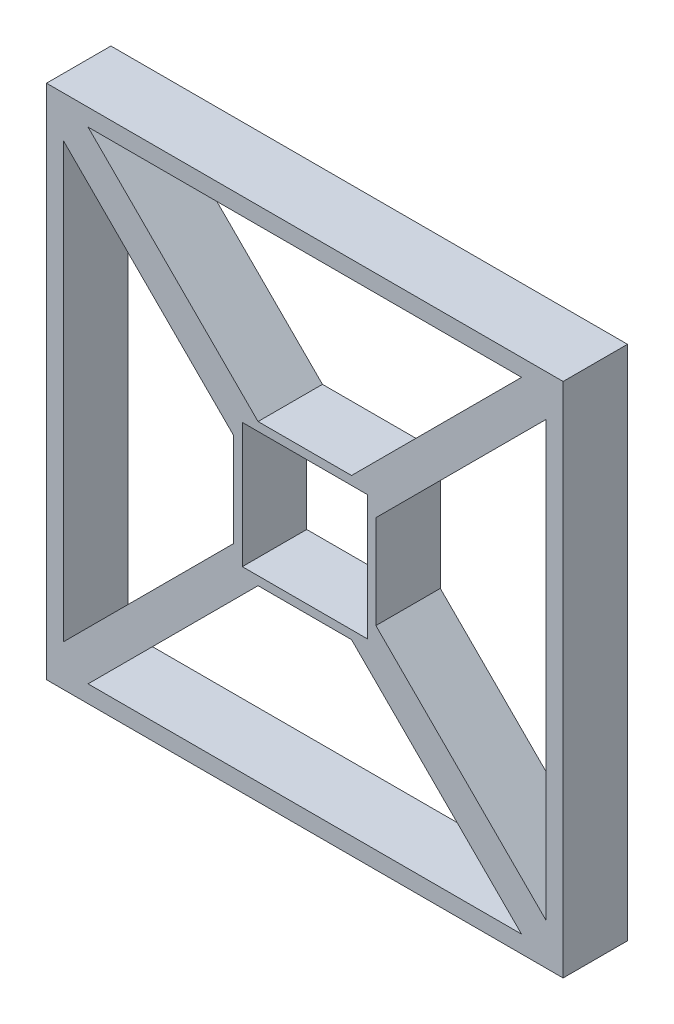
SolidWorks part; units mm, degrees
ref_plane "Front Plane" through (0, 0, 0) normal (0, 0, 1) x (1, 0, 0)
ref_plane "Top Plane" through (0, 0, 0) normal (0, 1, 0) x (1, 0, 0)
ref_plane "Right Plane" through (0, 0, 0) normal (1, 0, 0) x (0, 0, -1)
sketch "Sketch1" plane through (0, 0, 0) normal (0, 0, 1) x (1, 0, 0)
  line L0 (-2517.1573, 2800) -> (2517.1573, 2800)
  line L1 (-3000, 3000) -> (3000, 3000)
  line L2 (-3000, 3000) -> (-3000, -3000)
  line L3 (-3000, -3000) -> (3000, -3000)
  line L4 (3000, 3000) -> (3000, -3000)
  line L5 (-2800, 2800) -> (-2800, -2800) construction
  line L6 (-2800, 2800) -> (2800, 2800) construction
  line L7 (2800, 2517.1573) -> (2800, -2517.1573)
  line L8 (-2517.1573, -2800) -> (2517.1573, -2800)
  line L9 (-2800, 2517.1573) -> (-2800, -2517.1573)
  line L10 (-2517.1573, -2800) -> (-542.7684, -825.6111)
  line L11 (-2800, -2517.1573) -> (-825.6111, -542.7684)
  line L12 (-2800, 2517.1573) -> (-825.6111, 542.7684)
  line L13 (-2517.1573, 2800) -> (-542.7684, 825.6111)
  line L14 (-542.7684, 825.6111) -> (542.7684, 825.6111)
  line L15 (-725.6111, 725.6111) -> (725.6111, 725.6111)
  line L16 (-725.6111, 725.6111) -> (-725.6111, -725.6111)
  line L17 (-725.6111, -725.6111) -> (725.6111, -725.6111)
  line L18 (725.6111, 725.6111) -> (725.6111, -725.6111)
  line L19 (-2800, -2800) -> (2800, -2800) construction
  line L20 (2800, 2800) -> (2800, -2800) construction
  line L21 (825.6111, 542.7684) -> (825.6111, -542.7684)
  line L22 (-542.7684, -825.6111) -> (542.7684, -825.6111)
  line L23 (-825.6111, 542.7684) -> (-825.6111, -542.7684)
  line L24 (542.7684, 825.6111) -> (2517.1573, 2800)
  line L25 (825.6111, 542.7684) -> (2800, 2517.1573)
  line L26 (825.6111, -542.7684) -> (2800, -2517.1573)
  line L27 (542.7684, -825.6111) -> (2517.1573, -2800)
  line L28 (-825.6111, 825.6111) -> (825.6111, 825.6111) construction
  line L29 (-825.6111, 825.6111) -> (-825.6111, -825.6111) construction
  line L30 (-825.6111, -825.6111) -> (825.6111, -825.6111) construction
  line L31 (825.6111, 825.6111) -> (825.6111, -825.6111) construction
  point P0 (0, 0)
  point P18 (0, 0)
  dimension "D1" = 200
  dimension "D6" = 100
extrude "Boss-Extrude1" add sketch "Sketch1" along normal blind 748 contours L27 L8 L10 L22 | L2 L3 L4 L1 | L16 L17 L18 L15 | L25 L7 L26 L21 | L9 L11 L23 L12 | L13 L14 L24 L0
